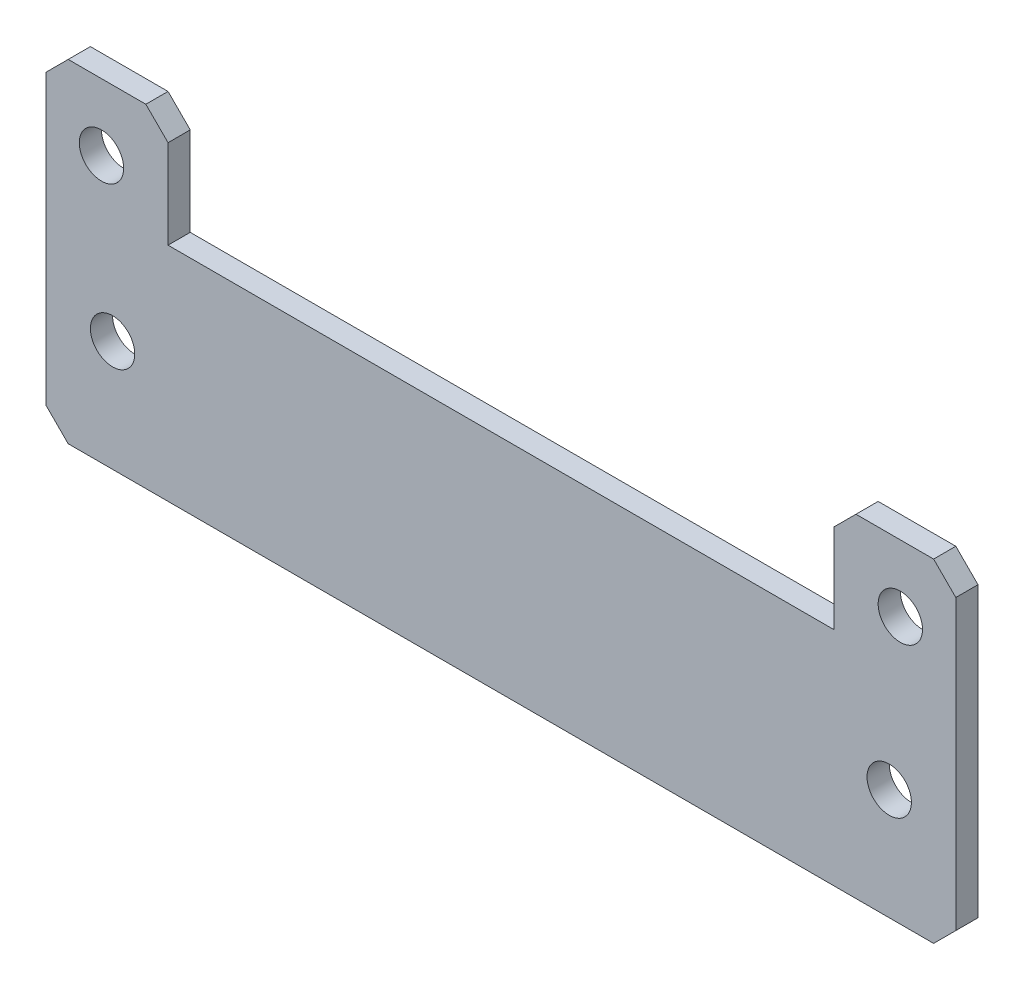
SolidWorks part; units mm, degrees
ref_plane "Ön Düzlem" through (0, 0, 0) normal (0, 0, 1) x (1, 0, 0)
ref_plane "Üst Düzlem" through (0, 0, 0) normal (0, 1, 0) x (1, 0, 0)
ref_plane "Sağ Düzlem" through (0, 0, 0) normal (1, 0, 0) x (0, 0, -1)
sketch "Sketch1" plane through (0, 0, 0) normal (0, 0, 1) x (1, 0, 0)
  line L0 (-39, 0) -> (39, 0)
  line L1 (41, 2) -> (41, 28)
  line L2 (39, 30) -> (32, 30)
  line L3 (30, 28) -> (30, 20)
  line L4 (30, 20) -> (-30, 20)
  line L5 (0, 20) -> (0, 0)
  line L6 (-30, 28) -> (-30, 20)
  line L7 (-39, 30) -> (-32, 30)
  line L8 (-41, 2) -> (-41, 28)
  line L9 (-41, 28) -> (-39, 30)
  line L10 (-39, 0) -> (-41, 2)
  line L11 (39, 0) -> (41, 2)
  line L12 (41, 28) -> (39, 30)
  line L13 (32, 30) -> (30, 28)
  line L14 (-32, 30) -> (-30, 28)
  point P1 (41, 0)
  point P4 (41, 30)
  point P5 (30, 30)
  point P8 (-30, 30)
  point P9 (-41, 30)
  point P10 (-41, 0)
  dimension "D1" = 41
  dimension "D2" = 30
  dimension "D3" = 11
  dimension "D4" = 10
extrude "Boss-Extrude1" add sketch "Sketch1" along normal blind 2 contours L14 L7 L9 L8 L10 L0 L5 L4 L6 | L2 L13 L3 L4 L5 L0 L11 L1 L12
sketch "Sketch2" plane through (0, 0, 2) normal (0, 0, 1) x (1, 0, 0)
  line L0 (-39, 0) -> (39, 0) construction
  line L1 (-41, 2) -> (-41, 28) construction
  circle A0 centre (-36, 24) radius 2
  circle A1 centre (36, 24) radius 2
  dimension "D1" = 4
  dimension "D2" = 72
  dimension "D3" = 24
  dimension "D4" = 5
extrude "Cut-Extrude1" cut sketch "Sketch2" against normal blind 2
sketch "Sketch3" plane through (0, 0, 0) normal (0, 0, -1) x (-1, 0, 0)
  line L0 (41, 2) -> (41, 28) construction
  line L1 (-41, 2) -> (-41, 28) construction
  line L2 (39, 0) -> (-39, 0) construction
  circle A0 centre (-35, 10) radius 2
  circle A1 centre (35, 10) radius 2
  dimension "D1" = 4
  dimension "D2" = 6
  dimension "D3" = 6
  dimension "D4" = 10
extrude "Cut-Extrude2" cut sketch "Sketch3" against normal blind 2
